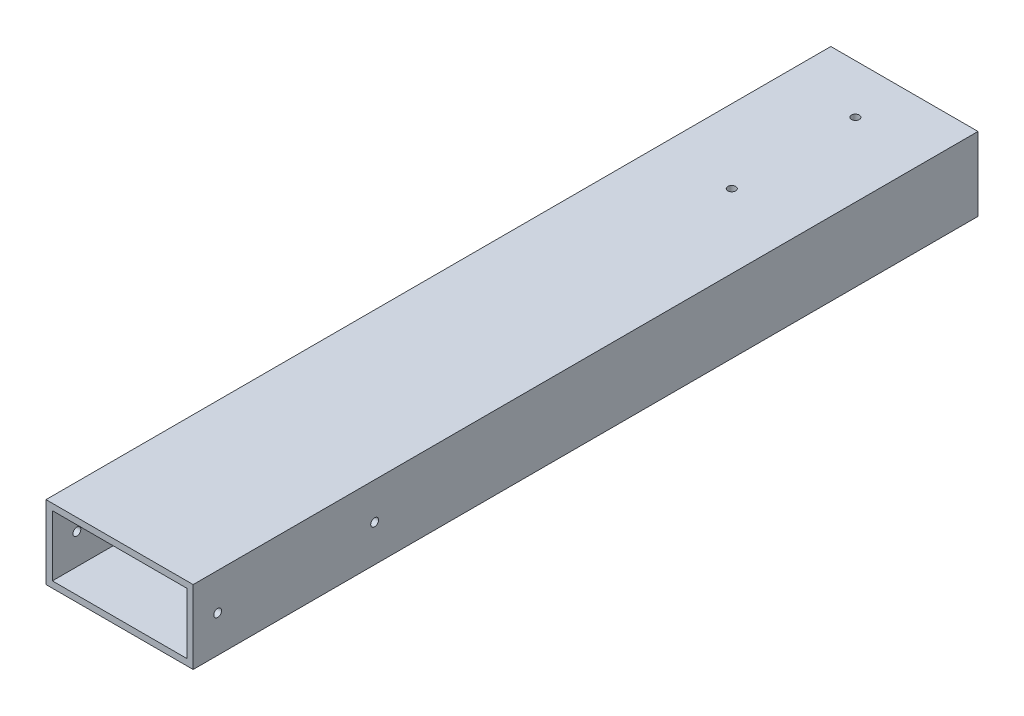
SolidWorks part; units mm, degrees
ref_plane "Front Plane" through (0, 0, 0) normal (0, 0, 1) x (1, 0, 0)
ref_plane "Top Plane" through (0, 0, 0) normal (0, 1, 0) x (1, 0, 0)
ref_plane "Right Plane" through (0, 0, 0) normal (1, 0, 0) x (0, 0, -1)
sketch "Sketch2" plane through (0, 0, 0) normal (0, 0, 1) x (1, 0, 0)
  line L1 (-19.05, 9.525) -> (19.05, 9.525)
  line L2 (-19.05, 9.525) -> (-19.05, -9.525)
  line L3 (-19.05, -9.525) -> (19.05, -9.525)
  line L4 (19.05, 9.525) -> (19.05, -9.525)
  line L5 (-17.399, 7.874) -> (17.399, 7.874)
  line L6 (-17.399, 7.874) -> (-17.399, -7.874)
  line L7 (-17.399, -7.874) -> (17.399, -7.874)
  line L8 (17.399, 7.874) -> (17.399, -7.874)
  point P8 (0, 7.874)
  point P9 (0, 9.525)
  point P11 (-19.05, 0)
  point P12 (-17.399, 0)
  dimension "D1" = 38.1
  dimension "D2" = 19.05
  dimension "D3" = 1.651
  dimension "D4" = 1.651
extrude "Boss-Extrude1" add sketch "Sketch2" along normal blind 203.2
sketch "Sketch3" plane through (19.05, 0, 0) normal (1, 0, 0) x (0, 0, -1)
  line L0 (-203.2, -9.525) -> (-203.2, 9.525) construction
  circle A0 centre (-196.85, 0) radius 1.016
  circle A1 centre (-156.21, 0) radius 1.016
  point P6 (-203.2, 0)
  dimension "D3" = 2.032
  dimension "D1" = 40.64
  dimension "D2" = 6.35
extrude "Cut-Extrude1" cut sketch "Sketch3" against normal through all
sketch "Sketch6" plane through (0, 9.525, 0) normal (0, 1, 0) x (1, 0, 0)
  line L0 (19.05, 0) -> (-19.05, 0) construction
  circle A0 centre (0, -12.7) radius 1.016
  circle A1 centre (0, -44.704) radius 1.016
  point P6 (0, 0)
  dimension "D1" = 2.032
  dimension "D2" = 12.7
extrude "Cut-Extrude2" cut sketch "Sketch6" against normal up to next
